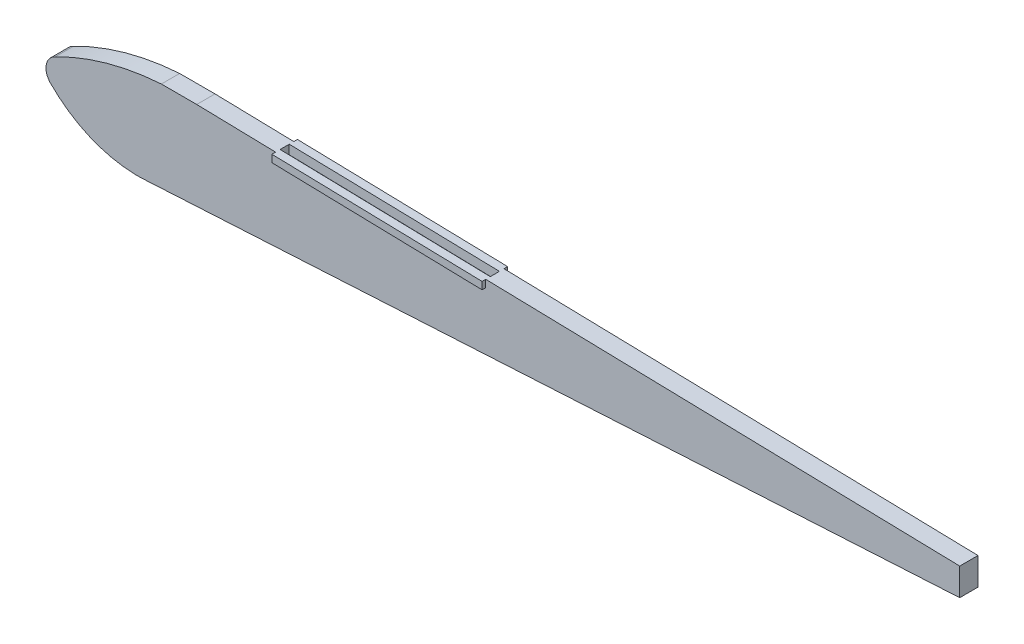
SolidWorks part; units mm, degrees
material "Balsa"
ref_plane "Front Plane" through (0, 0, 0) normal (0, 0, 1) x (1, 0, 0)
ref_plane "Top Plane" through (0, 0, 0) normal (0, 1, 0) x (1, 0, 0)
ref_plane "Right Plane" through (0, 0, 0) normal (1, 0, 0) x (0, 0, -1)
sketch "Sketch1" plane through (0, 0, 0) normal (0, 0, 1) x (1, 0, 0)
  line L0 (0, 0) -> (566.7048, 0) construction
  line L2 (33.3524, 25) -> (533.3524, 25)
  line L3 (33.3524, 25) -> (33.3524, -25)
  line L4 (33.3524, -25) -> (533.3524, -25)
  line L5 (533.3524, 25) -> (533.3524, -25)
  line L6 (33.3524, 25) -> (533.3524, -25) construction
  line L7 (33.3524, -25) -> (533.3524, 25) construction
  point P3 (283.3524, 0)
  dimension "D1" = 500
  dimension "D2" = 50
extrude "Boss-Extrude1" add sketch "Sketch1" along normal blind 10
sketch "Sketch2" plane through (0, 0, 10) normal (0, 0, 1) x (1, 0, 0)
  line L0 (33.3524, 0) -> (158.3524, 0) construction
  line L1 (33.3524, 25) -> (33.3524, -25) construction
  line L2 (33.3524, -25) -> (533.3524, -25) construction
  line L4 (533.3524, 25) -> (33.3524, 25) construction
  line L5 (85.6278, -25) -> (533.3524, 0)
  line L6 (533.3524, -25) -> (533.3524, 25) construction
  line L7 (533.3524, 0) -> (533.3524, 15)
  line L8 (533.3524, 15) -> (115.9051, 25)
  line L9 (533.3524, 15) -> (533.3524, 0)
  arc A0 (35.7524, -4.8141) -> (85.6278, -25) centre (83.8104, 42.2185) ccw
  arc A2 (38.4047, 8.8099) -> (115.9051, 25) centre (106.2209, -122.2304) cw
  arc A3 (38.4047, 8.8099) -> (35.7524, -4.8141) centre (41.9407, 1.0513) ccw
  line M8 (533.3524, -25) -> (533.3524, 25)
  line M9 (533.3524, 25) -> (33.3524, 25)
  line M10 (33.3524, 25) -> (33.3524, -25)
  line M11 (33.3524, -25) -> (533.3524, -25)
  dimension "D2" = 15
  dimension "D1" = 125
extrude "Cut-Extrude1" cut sketch "Sketch2" against normal through all contours L0 A0 A3 M10 M11 | L0 A3 A2 M10 M9 | L5 M11 M8 | L8 M8 M9
sketch "Sketch3" plane through (0, 0, 0) normal (0, 0, -1) x (-1, 0, 0)
  line L0 (0, 0) -> (-533.3524, 0) construction
  line L1 (-33.4144, 1.0513) -> (-158.4144, 0) construction
  line L2 (-159.0032, 23.9676) -> (-274.0032, 21.2127)
  line L3 (-533.3524, 15) -> (-115.9051, 25) construction
  line L4 (-274.0032, 21.2127) -> (-274.0032, 17.2127)
  line L5 (-274.0032, 17.2127) -> (-159.0032, 19.9676)
  line L6 (-159.0032, 19.9676) -> (-159.0032, 23.9676)
  arc A0 (-35.7524, -4.8141) -> (-38.4047, 8.8099) centre (-41.9407, 1.0513) ccw construction
  dimension "D1" = 125
  dimension "D2" = 4
  dimension "D3" = 115
extrude "Boss-Extrude3" add sketch "Sketch3" along normal blind 2 and the other way blind 12
sketch "Sketch4" plane through (0.665, 27.7606, 0) normal (0.0239, 0.9997, 0) x (0.9997, -0.0239, 0)
  line L0 (158.3836, 0) -> (158.3836, -10) construction
  line L1 (158.3836, -5) -> (273.4166, -5) construction
  line L2 (273.4166, 0) -> (273.4166, -10) construction
  line L4 (158.3836, -2.5) -> (273.4166, -2.5)
  line L5 (158.3836, -2.5) -> (158.3836, -7.5)
  line L6 (158.3836, -7.5) -> (273.4166, -7.5)
  line L7 (273.4166, -2.5) -> (273.4166, -7.5)
  line L8 (158.3836, -2.5) -> (273.4166, -7.5) construction
  line L9 (158.3836, -7.5) -> (273.4166, -2.5) construction
  point P10 (215.9001, -5)
  dimension "D1" = 5
extrude "Cut-Extrude2" cut sketch "Sketch4" against normal blind 5
